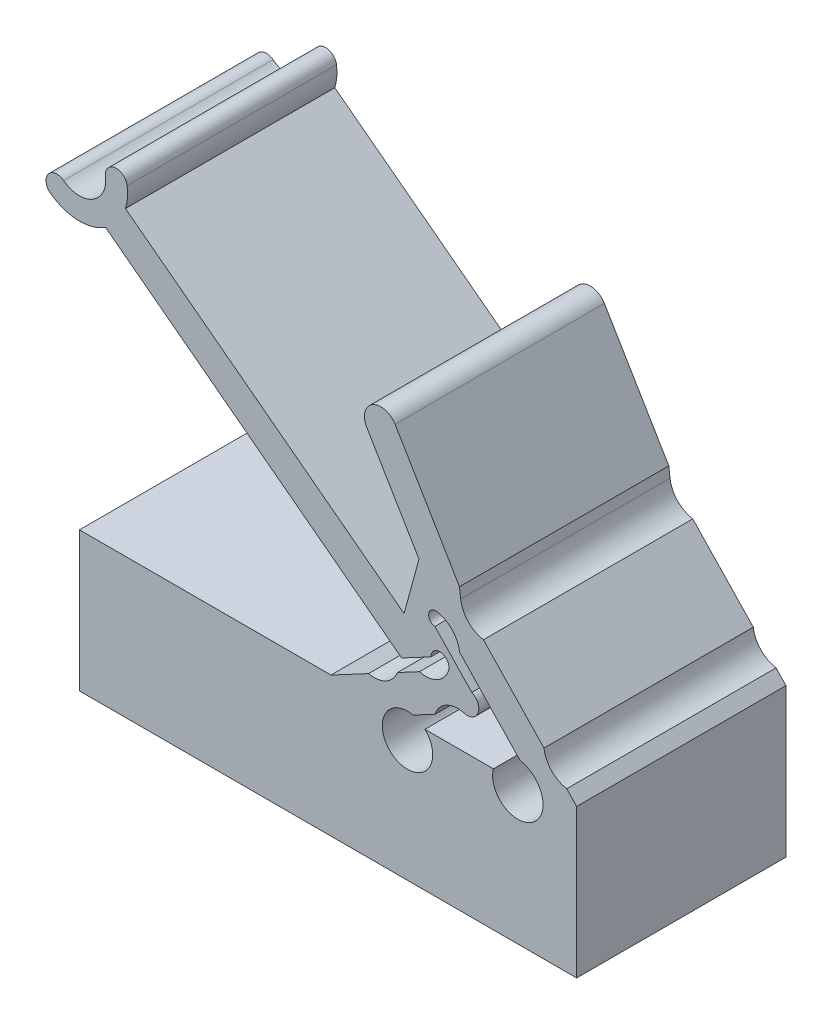
SolidWorks part; units mm, degrees
ref_plane "Front Plane" through (0, 0, 0) normal (0, 0, 1) x (1, 0, 0)
ref_plane "Top Plane" through (0, 0, 0) normal (0, 1, 0) x (1, 0, 0)
ref_plane "Right Plane" through (0, 0, 0) normal (1, 0, 0) x (0, 0, -1)
sketch "Sketch-SkeletonConfigUp" plane through (0, 0, 0) normal (0, 0, 1) x (1, 0, 0)
  line L0 (0, 0) -> (0, -50000) construction
  line L1 (0, 0) -> (7.455, 0.2734) construction
  line L2 (9.9233, 0.3639) -> (10.6101, 4.558) construction
  line L3 (10.6101, 4.558) -> (7.9471, 2.8569) construction
  line L4 (7.9471, 2.8569) -> (7.455, 0.2734) construction
  line L5 (10.6101, 4.558) -> (12.0093, 11.478) construction
  line L6 (7.9471, 2.8569) -> (4.1146, 23.199) construction
  line L7 (7.455, 0.2734) -> (9.9233, 0.3639) construction
  line L8 (-989.4051, -36.2798) -> (9.9233, 0.3639) construction
  dimension "D2" = 7.46
  dimension "D3" = 2.47
  dimension "D4" = 4.25
  dimension "D5" = 78.6
  dimension "D6" = 3.16
  dimension "D7" = 7.06
  dimension "D8" = 20.7
  dimension "D9" = 2.63
  dimension "D10" = 46
  dimension "D11" = 111.9
  dimension "D12" = 92.1
sketch "Sketch-SkeletonConfigDown" plane through (0, 0, 0) normal (0, 0, 1) x (1, 0, 0)
  line L0 (0, 0) -> (0, -50000) construction
  line L1 (0, 0) -> (7.455, 0.2734) construction
  line L2 (9.9233, 0.3639) -> (10.6101, 4.558) construction
  line L3 (10.6101, 4.558) -> (9.7761, 1.5101) construction
  line L4 (9.7761, 1.5101) -> (7.455, 0.2734) construction
  line L5 (10.6101, 4.558) -> (7.0062, 10.6288) construction
  line L6 (9.7761, 1.5101) -> (-6.7111, 14.0265) construction
  line L7 (7.455, 0.2734) -> (9.9233, 0.3639) construction
  line L8 (-993.745, -36.439) -> (9.9233, 0.3639) construction
  dimension "D2" = 7.46
  dimension "D3" = 2.47
  dimension "D4" = 4.25
  dimension "D5" = 78.6
  dimension "D6" = 3.16
  dimension "D7" = 7.06
  dimension "D8" = 20.7
  dimension "D9" = 2.63
  dimension "D10" = 46
  dimension "D11" = 111.9
  dimension "D1" = 92.1
sketch "Sketch-ConfigDown" plane through (0, 0, 0) normal (0, 0, 1) x (1, 0, 0)
  line L3 (7.5456, -0.2237) -> (4.7337, -0.3268) construction
  line L4 (9.7761, 1.5101) -> (-6.7111, 14.0265) construction
  line L6 (-200859.4238, -7365.1807) -> (9.9233, 0.3639) construction
  line L7 (7.5456, -0.2237) -> (15.9124, 0.0831) construction
  line L9 (7.455, 0.2734) -> (9.9233, 0.3639) construction
  line L10 (10.9008, 0.9001) -> (10.9374, -0.0993) construction
  line L15 (9.4668, 0.4955) -> (8.4696, -0.0359)
  line L18 (8.3945, 1.6237) -> (9.0998, 0.2999) construction
  line L19 (6.3613, 10.246) -> (8.7382, 6.242)
  line L20 (-5.5253, 12.1846) -> (7.951, 1.954)
  line L21 (8.058, 3.756) -> (-4.6183, 13.3794)
  line L22 (9.7761, 1.5101) -> (7.455, 0.2734) construction
  line L23 (2.778, 5.8811) -> (3.685, 7.0758) construction
  line L26 (10.6101, 4.558) -> (14.4503, 0.5299) construction
  line L27 (10.0779, 5.4546) -> (9.138, 2.0199) construction
  line L28 (11.1921, 5.0345) -> (15.9124, 0.0831) construction
  line L29 (14.3752, -0.4783) -> (10.5848, 3.4977) construction
  line L30 (12.8128, 1.1606) -> (13.8985, 2.1956) construction
  line L34 (4.7337, -0.3268) -> (4.7337, -6.6768) construction
  line L36 (4.7337, -6.6768) -> (15.9124, -6.6768)
  line L37 (15.9124, -6.6768) -> (15.9124, 0.0831)
  line L38 (-8.0357, 12.2817) -> (-6.0162, 14.9419) construction
  line L39 (10.6101, 4.558) -> (9.7761, 1.5101) construction
  line L40 (9.5145, 3.3957) -> (10.9613, 2.9997) construction
  line L42 (7.6511, 11.0117) -> (10.5812, 6.0759)
  line L43 (7.8883, 7.6738) -> (9.1781, 8.4395) construction
  line L44 (10.6101, 4.558) -> (7.0062, 10.6288) construction
  line L45 (9.01, -0.3268) -> (4.7337, -0.3268) construction
  line L46 (14.3752, -0.4783) -> (15.9124, -0.4783) construction
  line L47 (12.1252, -0.3268) -> (9.01, -0.3268)
  line L48 (8.7382, 6.242) -> (8.058, 3.756)
  line L49 (15.9124, 0.0831) -> (15.4609, 0.5567)
  line L50 (10.5848, 3.4977) -> (9.5498, 4.5833) construction
  line L51 (15.4609, 0.5567) -> (14.3752, -0.4783) construction
  line L52 (14.7625, 0.927) -> (14.9434, 1.0995) construction
  line L53 (13.3402, 0.6074) -> (14.4259, 1.6424) construction
  line L54 (11.1921, 5.0345) -> (10.6355, 5.6184) construction
  line L55 (10.972, 4.903) -> (11.153, 5.0755) construction
  line L56 (9.5498, 4.5833) -> (10.6355, 5.6184) construction
  line L57 (10.5848, 3.4977) -> (11.6705, 4.5327) construction
  line L58 (10.972, 4.903) -> (10.2482, 4.213) construction
  line L59 (11.6705, 4.5327) -> (14.4259, 1.6424)
  line L60 (13.3402, 0.6074) -> (10.5848, 3.4977)
  line L61 (10.6355, 5.6184) -> (10.5812, 6.0759)
  line L62 (7.2336, 0.6889) -> (7.116, 0.9096) construction
  line L63 (7.1458, -0.7412) -> (6.4216, -1.127) construction
  line L64 (7.7642, 1.2879) -> (8.4696, -0.0359) construction
  line L65 (6.4404, 0.5826) -> (7.1458, -0.7412) construction
  line L66 (6.4404, 0.5826) -> (4.7337, -0.3268)
  line L67 (6.4404, 0.5826) -> (7.7642, 1.2879) construction
  line L68 (7.2336, 0.6889) -> (7.6764, -0.1422) construction
  line L69 (10.0853, 2.5247) -> (10.6904, 2.847) construction
  line L70 (10.7907, 1.2008) -> (11.23, 1.4349) construction
  line L71 (9.5656, 1.9051) -> (9.448, 2.1258) construction
  line L72 (8.7615, 1.8193) -> (9.4668, 0.4955) construction
  line L73 (10.0853, 2.5247) -> (10.7907, 1.2008) construction
  line L74 (9.5656, 1.9051) -> (9.9866, 1.115) construction
  line L75 (7.7642, 1.2879) -> (8.7615, 1.8193)
  line L76 (7.951, 1.954) -> (9.2771, 2.6606)
  line L77 (9.4607, 3.9522) -> (10.9702, 2.3688)
  line L78 (10.9702, 2.3688) -> (11.1406, 2.19)
  line L79 (-6.7111, 14.0265) -> (-5.0362, 14.2558) construction
  line L80 (-6.7111, 14.0265) -> (-6.7111, -6.6768) construction
  line L81 (4.7337, -6.6768) -> (-6.7111, -6.6768)
  line L82 (-6.7111, -6.6768) -> (-6.7111, -0.3268)
  line L83 (-6.7111, -0.3268) -> (4.7337, -0.3268)
  line L84 (8.7615, 1.8193) -> (10.0853, 2.5247) construction
  arc A2 (-7.4311, 13.0782) -> (-5.5316, 14.188) centre (-6.7111, 14.0265) ccw
  arc A3 (-4.6183, 13.3794) -> (-4.5408, 14.3236) centre (-6.7111, 14.0265) ccw
  arc A4 (-8.0357, 12.2817) -> (-7.4311, 13.0782) centre (-7.7334, 12.68) cw
  arc A5 (-4.5408, 14.3236) -> (-5.5316, 14.188) centre (-5.0362, 14.2558) ccw
  arc A6 (-8.0357, 12.2817) -> (-5.5253, 12.1846) centre (-6.7111, 14.0265) ccw
  arc A7 (6.3613, 10.246) -> (7.6511, 11.0117) centre (7.0062, 10.6288) cw
  arc A8 (15.4609, 0.5567) -> (14.4259, 1.6424) centre (15.6672, 1.7896) cw
  arc A9 (14.3752, -0.4783) -> (13.3402, 0.6074) centre (13.1339, -0.6255) ccw
  arc A10 (10.6355, 5.6184) -> (11.6705, 4.5327) centre (11.8768, 5.7655) ccw
  arc A11 (9.5498, 4.5833) -> (10.5848, 3.4977) centre (9.3435, 3.3505) cw
  arc A12 (7.7642, 1.2879) -> (6.4404, 0.5826) centre (6.6941, 1.7014) cw
  arc A13 (7.1458, -0.7412) -> (8.4696, -0.0359) centre (8.2159, -1.1547) cw
  arc A14 (7.1458, -0.7412) -> (9.01, -0.3268) centre (8.2159, -1.1547) ccw
  arc A15 (8.7615, 1.8193) -> (10.0853, 2.5247) centre (9.0571, 2.8595) ccw
  arc A16 (9.4668, 0.4955) -> (10.7907, 1.2008) centre (10.4951, 0.1606) cw
  arc A19 (10.0853, 2.5247) -> (9.2771, 2.6606) centre (9.6914, 2.6529) ccw
  arc A20 (14.3752, -0.4783) -> (12.1252, -0.3268) centre (13.236, -0.6134) cw
  arc A21 (9.5498, 4.5833) -> (9.4607, 3.9522) centre (9.4972, 4.2689) ccw
  arc A22 (10.7907, 1.2008) -> (11.1406, 2.19) centre (10.9343, 1.7065) ccw
  point P24 (8.7471, 0.9618)
  point P28 (10.9191, 0.4004)
  point P30 (8.5332, 8.0566)
  point P43 (10.2379, 3.1977)
  point P47 (14.7625, 0.927)
  point P51 (3.2315, 6.4785)
  point P61 (13.3557, 1.6781)
  dimension "D1" = 1
  dimension "D8" = 1.5
  dimension "D12" = 1.5
  dimension "D3" = 2.3812
  dimension "D4" = 4.3812
  dimension "D5" = 1.5
  dimension "D6" = 7
  dimension "D2" = 6.35
  dimension "D7" = 1.5
  dimension "D9" = 1.5
  dimension "D10" = 0.25
  dimension "D11" = 1.5
  dimension "D13" = 0.5
  dimension "D14" = 0.5
  dimension "D15" = 45
extrude "Boss-ConfigDown" add sketch "Sketch-ConfigDown" along normal blind 9.525 separate body
sketch "Sketch-ConfigUp" [suppressed] plane through (0, 0, 0) normal (0, 0, 1) x (1, 0, 0)
  line L1 (7.3156, 2.2137) -> (7.1042, 1.1037)
  line L2 (8.0635, 0.796) -> (13.3219, 0.9888) construction
  line L3 (10.1988, -0.1264) -> (6.8464, -0.2493) construction
  line L4 (7.9471, 2.8569) -> (7.455, 0.2734) construction
  line L5 (11.5192, 11.5771) -> (10.5754, 6.909)
  line L6 (7.455, 0.2734) -> (9.9233, 0.3639) construction
  line L7 (10.1988, -0.1264) -> (15.5786, 0.0709) construction
  line L9 (10.6101, 4.558) -> (7.9471, 2.8569) construction
  line L10 (8.9451, 0.8283) -> (8.9817, -0.171) construction
  line L11 (7.2099, 1.6587) -> (8.1922, 1.4716) construction
  line L12 (8.7452, 3.96) -> (9.2835, 3.1173) construction
  line L15 (9.9233, 0.3639) -> (10.6101, 4.558) construction
  line L16 (9.7754, 2.5547) -> (10.7623, 2.3931) construction
  line L17 (12.4994, 11.3789) -> (11.2863, 5.379)
  line L18 (10.6101, 4.558) -> (12.0093, 11.478) construction
  line L19 (10.5058, 6.5648) -> (11.486, 6.3666) construction
  line L20 (4.0182, 21.0106) -> (7.1163, 4.5661)
  line L21 (8.0021, 5.2653) -> (5.0009, 21.1957)
  line L22 (7.9471, 2.8569) -> (4.1146, 23.199) construction
  line L23 (6.0985, 9.9681) -> (7.0813, 10.1533) construction
  line L24 (8.3015, 3.6766) -> (10.1621, 4.8651) construction
  line L26 (10.6101, 4.558) -> (14.4503, 0.5299) construction
  line L27 (-200855.0838, -7365.0216) -> (9.9233, 0.3639) construction
  line L30 (10.7658, 3.6702) -> (11.4896, 4.3602) construction
  line L34 (6.8464, -0.2493) -> (6.8464, -3.4808) construction
  line L38 (1.9619, 22.7935) -> (4.1146, 23.199) construction
  line L39 (4.1146, 23.199) -> (5.9236, 21.9636) construction
  line L40 (13.528, -0.3058) -> (7.7789, -0.3058) construction
  line L41 (13.528, -0.3058) -> (7.7789, -0.3058)
  line L42 (11.2489, 5.194) -> (10.7354, 2.6543) construction
  line L43 (10.1621, 4.8651) -> (9.715, 2.6538) construction
  line L44 (6.8464, -0.2493) -> (5.1916, -0.31) construction
  line L45 (8.0635, 0.796) -> (8.0865, 0.9166) construction
  line L46 (8.0635, 0.796) -> (7.8058, -0.5569) construction
  line L47 (7.2094, 0.3201) -> (6.9638, 0.3669) construction
  line L48 (7.2094, 0.3201) -> (7.7006, 0.2266) construction
  line L49 (6.8235, -0.3698) -> (7.8058, -0.5569) construction
  line L50 (7.4382, 2.8574) -> (7.5963, 3.6872) construction
  line L51 (8.3979, 2.5516) -> (8.5786, 3.5001) construction
  line L52 (7.3156, 2.2137) -> (8.2979, 2.0266) construction
  line L53 (7.5963, 3.6872) -> (8.5786, 3.5001) construction
  line L54 (7.7015, 2.9037) -> (8.1927, 2.8101) construction
  line L55 (7.7015, 2.9037) -> (7.4559, 2.9505) construction
  line L56 (8.1564, 2.8991) -> (7.6708, 3.0185) construction
  line L57 (7.1163, 4.5661) -> (7.4382, 2.8574) construction
  line L58 (11.2863, 5.379) -> (10.3061, 5.5772) construction
  line L59 (7.4382, 2.8574) -> (7.3156, 2.2137) construction
  line L60 (7.8068, 2.1202) -> (8.6839, 3.337) construction
  line L61 (8.2979, 2.0266) -> (8.0865, 0.9166)
  line L62 (7.1042, 1.1037) -> (8.0865, 0.9166) construction
  line L69 (10.8552, 4.5085) -> (11.1002, 4.4589) construction
  line L70 (7.7789, -0.3058) -> (5.3047, -0.3058) construction
  line L71 (7.7789, -0.3058) -> (5.3047, -0.3058) construction
  line L73 (7.1042, 1.1037) -> (6.8464, -0.2493) construction
  line L74 (10.2687, 5.3922) -> (11.2489, 5.194) construction
  line L75 (9.9714, 3.922) -> (10.9516, 3.7238) construction
  line L76 (10.8552, 4.5085) -> (10.3651, 4.6076) construction
  line L77 (8.3979, 2.5516) -> (8.2979, 2.0266) construction
  line L78 (9.5833, 3.3088) -> (8.3979, 2.5516) construction
  line L79 (8.0021, 5.2653) -> (10.5754, 6.909)
  line L80 (8.0021, 5.2653) -> (8.3015, 3.6766) construction
  line L81 (10.5058, 6.5648) -> (10.1621, 4.8651) construction
  line L82 (10.5058, 6.5648) -> (10.5754, 6.909) construction
  line L83 (11.4896, 4.3602) -> (10.7658, 3.6702) construction
  line L84 (11.1158, 4.8153) -> (10.6255, 4.7174) construction
  line L85 (6.5762, 10.3736) -> (9.0074, 6.2784)
  line L86 (9.0074, 6.2784) -> (8.2015, 3.3332)
  line L87 (8.2015, 3.3332) -> (-4.7101, 13.1352)
  line L88 (-5.3148, 12.3387) -> (8.4132, 1.917)
  line L89 (8.4132, 1.917) -> (9.4143, 2.4504)
  line L90 (8.8791, 1.5987) -> (7.8818, 1.0673)
  line L91 (6.558, 0.362) -> (5.3047, -0.3058)
  line L92 (5.3047, -0.3058) -> (-6.7111, -0.3058)
  line L93 (-6.7111, -0.3058) -> (-6.7111, -3.4808)
  line L94 (-6.7111, -3.4808) -> (15.5786, -3.4808)
  line L95 (15.5786, -3.4808) -> (15.5786, 0.0709)
  line L96 (15.5786, 0.0709) -> (15.28, 0.3842)
  line L97 (14.2449, 1.4699) -> (11.4896, 4.3602)
  line L98 (10.4545, 5.4459) -> (10.4021, 5.8879)
  line L99 (10.4021, 5.8879) -> (7.4361, 10.8841)
  line L106 (6.558, 0.362) -> (5.3047, -0.3058)
  line L107 (5.3047, -0.3058) -> (-6.7111, -0.3058)
  line L108 (-6.7111, -0.3058) -> (-6.7111, -3.4808)
  line L109 (-6.7111, -3.4808) -> (15.5786, -3.4808)
  line L110 (15.5786, -3.4808) -> (15.5786, 0.0709)
  line L112 (15.5786, 0.0709) -> (11.4896, 4.3602)
  line L114 (11.1277, 4.0152) -> (10.7962, 5.4781) construction
  line L115 (9.5833, 3.3088) -> (10.5323, 3.915) construction
  line L116 (13.3219, 0.9888) -> (10.7658, 3.6702)
  line L117 (10.7658, 3.6702) -> (10.5323, 3.915) construction
  line L118 (10.6101, 4.558) -> (7.9471, 2.8569) construction
  line L119 (8.6839, 3.337) -> (9.4161, 2.8092) construction
  line L120 (8.6839, 3.337) -> (7.8068, 3.9692) construction
  line L121 (9.0288, 3.0406) -> (8.2979, 2.0266) construction
  line L123 (9.7888, 5.7212) -> (8.6571, 4.9983)
  line L124 (8.5388, 4.5661) -> (9.2253, 3.2085)
  line L125 (9.0074, 6.2784) -> (8.2015, 3.3332) construction
  line L126 (13.3219, 0.9888) -> (14.1275, 0.1438)
  line L127 (11.2489, 5.194) -> (11.2863, 5.379) construction
  arc A0 (11.5192, 11.5771) -> (12.4994, 11.3789) centre (12.0093, 11.478) cw
  arc A2 (2.9446, 22.9786) -> (5.0978, 22.5276) centre (4.1146, 23.199) ccw
  arc A3 (5.0009, 21.1957) -> (5.9236, 21.9636) centre (4.1146, 23.199) ccw
  arc A4 (1.9619, 22.7935) -> (2.9446, 22.9786) centre (2.4533, 22.886) cw
  arc A5 (5.9236, 21.9636) -> (5.0978, 22.5276) centre (5.5107, 22.2456) ccw
  arc A6 (1.9619, 22.7935) -> (4.0182, 21.0106) centre (4.1146, 23.199) ccw
  arc A7 (13.528, -0.3058) -> (14.5562, -0.3058) centre (14.0421, -0.3668) ccw construction
  arc A8 (13.528, -0.3058) -> (14.1275, 0.1438) centre (14.0421, -0.3668) ccw
  arc A9 (7.1042, 1.1037) -> (6.8235, -0.3698) centre (5.9815, 0.554) cw construction
  arc A10 (7.8058, -0.5569) -> (8.0865, 0.9166) centre (8.9285, -0.0073) cw construction
  arc A11 (7.3156, 2.2137) -> (7.5963, 3.6872) centre (6.4736, 3.1376) ccw construction
  arc A12 (8.2979, 2.0266) -> (8.5786, 3.5001) centre (9.4206, 2.5762) cw construction
  arc A13 (11.2489, 5.194) -> (10.9516, 3.7238) centre (12.0804, 4.2607) ccw construction
  arc A14 (10.2687, 5.3922) -> (9.9714, 3.922) centre (9.1399, 4.8553) cw construction
  arc A15 (8.0865, 0.9166) -> (7.0282, -0.5206) centre (9.1391, -0.9668) ccw
  arc A16 (7.1042, 1.1037) -> (6.558, 0.362) centre (6.5823, 0.916) cw
  arc A17 (7.0282, -0.5206) -> (7.7789, -0.3058) centre (7.4604, -0.612) ccw
  arc A18 (11.4896, 4.3602) -> (11.2863, 5.379) centre (11.7287, 4.9376) cw
  arc A19 (8.2979, 2.0266) -> (9.0288, 3.0406) centre (8.6634, 2.5336) cw
  arc A21 (7.3156, 2.2137) -> (7.9864, 3.8397) centre (-8.9784, 9.887) ccw
  arc A22 (7.9864, 3.8397) -> (7.7104, 4.1617) centre (7.7563, 3.9218) ccw
  arc A23 (10.7658, 3.6702) -> (10.3061, 5.5772) centre (6.3229, 3.6081) ccw
  arc A24 (7.7104, 4.1617) -> (7.1163, 4.5661) centre (7.615, 4.66) cw
  arc A25 (9.0288, 3.0406) -> (9.2253, 3.2085) centre (9.1066, 3.1485) ccw
  arc A27 (10.3061, 5.5772) -> (9.7888, 5.7212) centre (9.9829, 5.4174) ccw
  arc A28 (7.4361, 10.8841) -> (6.5762, 10.3736) centre (7.0062, 10.6288) ccw
  arc A29 (-4.7101, 13.1352) -> (-4.5408, 14.3236) centre (-6.7111, 14.0265) ccw
  arc A30 (-4.5408, 14.3236) -> (-5.5316, 14.188) centre (-5.0362, 14.2558) ccw
  arc A31 (-7.4311, 13.0782) -> (-5.5316, 14.188) centre (-6.7111, 14.0265) ccw
  arc A32 (-7.4311, 13.0782) -> (-8.0357, 12.2817) centre (-7.7334, 12.68) ccw
  arc A33 (-8.0357, 12.2817) -> (-5.3148, 12.3387) centre (-6.7111, 14.0265) ccw
  arc A34 (10.2029, 2.304) -> (9.4143, 2.4504) centre (9.8276, 2.4796) ccw
  arc A35 (8.8791, 1.5987) -> (10.2029, 2.304) centre (9.0707, 2.8339) ccw
  arc A36 (6.558, 0.362) -> (7.8818, 1.0673) centre (6.7496, 1.5972) ccw
  arc A37 (14.2449, 1.4699) -> (15.28, 0.3842) centre (15.4863, 1.6171) ccw
  arc A38 (10.4545, 5.4459) -> (11.4896, 4.3602) centre (11.6958, 5.593) ccw
  arc A39 (8.6571, 4.9983) -> (8.5388, 4.5661) centre (8.8369, 4.7168) ccw
  point P25 (9.0144, 3.5387)
  point P27 (7.701, 1.5651)
  point P28 (8.9634, 0.3287)
  point P36 (10.2689, 2.4739)
  point P38 (10.9959, 6.4657)
  point P51 (6.5899, 10.0607)
  point P61 (11.1277, 4.0152)
  dimension "D3" = 3.175
  dimension "D4" = 6.175
  dimension "D13" = 0.625
  dimension "D17" = 0.625
  dimension "D1" = 1
  dimension "D5" = 7
  dimension "D10" = 1.5
  dimension "D11" = 0.25
  dimension "D8" = 1.5
  dimension "D9" = 0.25
  dimension "D6" = 1.5
  dimension "D7" = 0.25
  dimension "D12" = 1.5
  dimension "D15" = 0.5
  dimension "D16" = 1.5
  dimension "D18" = 0.5
  dimension "D19" = 25
  dimension "D20" = 1.5
  dimension "D14" = 45
  dimension "D2" = 0
extrude "Boss-ConfigUp" [suppressed] add sketch "Sketch-ConfigUp" along normal blind 9.525
sketch "Sketch2" [suppressed] plane through (0.0043, -0.3058, 0) normal (0, -1, 0) x (-1, 0, 0)
  line L0 (6.7155, 0) -> (-15.5743, 0) construction
  line L1 (-13.0304, 0) -> (-8.2679, 0)
  line L2 (-13.0304, 0) -> (-13.0304, -9.525)
  line L3 (-13.0304, -9.525) -> (-8.2679, -9.525)
  line L4 (-8.2679, 0) -> (-8.2679, -9.525)
  line L5 (-13.5237, 0) -> (-13.0304, 0) construction
  line L6 (6.7155, -9.525) -> (6.7155, 0) construction
  line L7 (-8.2679, 0) -> (-7.7746, 0) construction
  line L8 (-7.7746, 0) -> (-13.5237, 0) construction
  line L9 (6.7155, -9.525) -> (-15.5743, -9.525) construction
  line L10 (-15.5743, -4.7625) -> (6.7155, -4.7625) construction
  line L11 (-15.5743, -9.525) -> (-15.5743, 0) construction
  line L12 (-13.0304, 0) -> (-8.2679, -9.525) construction
  line L17 (-13.0304, -9.525) -> (-8.2679, 0) construction
  line L20 (3.5405, -9.525) -> (3.5405, 0)
  line L21 (3.5405, -9.525) -> (-1.222, -9.525)
  line L22 (3.5405, 0) -> (-1.222, 0)
  line L23 (-1.222, -9.525) -> (-1.222, 0)
  line L24 (3.5405, -9.525) -> (-1.222, 0) construction
  line L25 (3.5405, 0) -> (-1.222, -9.525) construction
  point P4 (-10.6492, -4.7625)
  point P12 (-14.5519, 0)
  point P26 (1.1592, -4.7625)
  dimension "D1" = 4.7625
  dimension "D2" = 3.175
extrude "Cut-NutSlot" [suppressed] cut sketch "Sketch2" along normal blind 1.5875
hole_wizard "#2 Clearance Hole1" [suppressed] positions "Sketch4" profile "Sketch3" hole size "#2" standard "ANSI Inch"
sketch "Sketch4" [suppressed] plane through (0, -3.4808, 0) normal (0, -1, 0) x (-1, 0, 0)
  line L16 (-13.0347, 0) -> (-8.2722, -9.525) construction
  point P40 (-10.6535, -4.7625)
  point P44 (1.1549, -4.7625)
sketch "Sketch3" plane through (10.6535, -3.4808, 4.7625) normal (1, 0, 0) x (0, 0, -1)
  line L0 (0, 0) -> (0, 1.5875)
  line L1 (0, 1.5875) -> (1.2192, 1.5875)
  line L2 (1.2192, 1.5875) -> (1.2192, 0)
  line L5 (1.2192, 0) -> (0, 0)
  line L11 (0, -6.35) -> (0, 107.95) construction
  dimension "Thru Hole Dia." = 2.4384
  dimension "Thru Hole Depth" = 1.5875
ref_plane "Plane-Midplane" [suppressed] through (0, 0, 4.7625) normal (0, 0, -1) x (-1, 0, 0)
equation "\"axle-diameter\"=2"
equation "\"switch-thickness\"=12"
equation "\"base-width\"=4.0"
equation "\"axle-bushing-radius\"=3"
equation "\"clearance\"= 0.25"
equation "\"arm-width\"=1.5"
equation "\"min-diameter\"=70"
equation "\"alpha\"=92.1"
equation "\"beta\"=26.0"
equation "\"gamma\"=78.6"
equation "\"delta\"=111.9"
equation "\"epsilon\"=46.0"
equation "\"eta\"=-228.1"
equation "\"l_AB\"=2.47"
equation "\"l_AC\"=2.63"
equation "\"l_BD\"=4.25"
equation "\"l_CD\"=3.16"
equation "\"l_CE\"=20.70"
equation "\"l_DF\"=7.06"
equation "\"l_OA\"=7.46"
equation "\"D2@Sketch-SkeletonConfigUp\" = \"l_OA\""
equation "\"D3@Sketch-SkeletonConfigUp\" = \"l_AB\""
equation "\"D4@Sketch-SkeletonConfigUp\" = \"l_BD\""
equation "\"D5@Sketch-SkeletonConfigUp\" = \"gamma\""
equation "\"D6@Sketch-SkeletonConfigUp\" = \"l_CD\""
equation "\"D7@Sketch-SkeletonConfigUp\" = \"l_DF\""
equation "\"D8@Sketch-SkeletonConfigUp\" = \"l_CE\""
equation "\"D9@Sketch-SkeletonConfigUp\" = \"l_AC\""
equation "\"D_groove\"=3.175"
equation "\"D3@Sketch-ConfigUp\" = \"D_groove\""
equation "\"D4@Sketch-ConfigUp\" = \"D_groove\" + 2 * \"arm-width\""
equation "\"D7@Sketch-SkeletonConfigDown\" = \"l_DF\""
equation "\"D6@Sketch-SkeletonConfigDown\" = \"l_CD\""
equation "\"D2@Sketch-SkeletonConfigDown\" = \"l_OA\""
equation "\"D3@Sketch-SkeletonConfigDown\" = \"l_AB\""
equation "\"D9@Sketch-SkeletonConfigDown\" = \"l_AC\""
equation "\"D8@Sketch-SkeletonConfigDown\" = \"l_CE\""
equation "\"D5@Sketch-SkeletonConfigDown\" = \"gamma\""
equation "\"D4@Sketch-SkeletonConfigDown\" = \"l_BD\""
equation "\"D1@Sketch-SkeletonConfigDown\" = \"alpha\""
equation "\"D5@Sketch-ConfigDown\" = \"arm-width\""
equation "\"hinge_length\"=1.5"
equation "\"hinge_depth\"=0.25"
equation "\"D9@Sketch-ConfigDown\" = \"hinge_length\""
equation "\"D10@Sketch-ConfigDown\" = \"hinge_depth\""
equation "\"D8@Sketch-ConfigDown\" = \"hinge_length\""
equation "\"D11@Sketch-ConfigDown\" = \"hinge_length\""
equation "\"D12@Sketch-ConfigDown\" = \"hinge_length\""
equation "\"D10@Sketch-ConfigUp\" = \"hinge_length\""
equation "\"D11@Sketch-ConfigUp\" = \"hinge_depth\""
equation "\"D8@Sketch-ConfigUp\" = \"hinge_length\""
equation "\"D9@Sketch-ConfigUp\" = \"hinge_depth\""
equation "\"D6@Sketch-ConfigUp\" = \"hinge_length\""
equation "\"D7@Sketch-ConfigUp\" = \"hinge_depth\""
equation "\"D10@Sketch-SkeletonConfigUp\"=\"epsilon\""
equation "\"D11@Sketch-SkeletonConfigUp\"=\"delta\""
equation "\"D12@Sketch-SkeletonConfigUp\"=\"alpha\""
equation "\"D11@Sketch-SkeletonConfigDown\"=\"delta\""
equation "\"D10@Sketch-SkeletonConfigDown\"=\"epsilon\""
equation "\"D15@Sketch-ConfigUp\"=2*\"hinge_depth\""
equation "\"D16@Sketch-ConfigUp\"=\"hinge_length\""
equation "\"D18@Sketch-ConfigUp\"=2*\"hinge_depth\""
equation "\"D20@Sketch-ConfigUp\"=\"hinge_length\""
